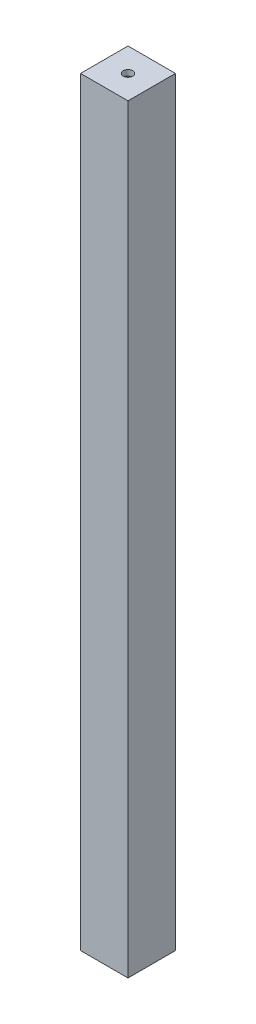
SolidWorks part; units mm, degrees
ref_plane "Front Plane" through (0, 0, 0) normal (0, 0, 1) x (1, 0, 0)
ref_plane "Top Plane" through (0, 0, 0) normal (0, 1, 0) x (1, 0, 0)
ref_plane "Right Plane" through (0, 0, 0) normal (1, 0, 0) x (0, 0, -1)
sketch "Sketch1" plane through (0, 0, 0) normal (0, 1, 0) x (1, 0, 0)
  line L1 (-12.5, 12.5) -> (12.5, 12.5)
  line L2 (-12.5, 12.5) -> (-12.5, -12.5)
  line L3 (-12.5, -12.5) -> (12.5, -12.5)
  line L4 (12.5, 12.5) -> (12.5, -12.5)
  line L5 (-12.5, 12.5) -> (12.5, -12.5) construction
  line L6 (-12.5, -12.5) -> (12.5, 12.5) construction
  point P0 (0, 0)
  dimension "D1" = 25
  dimension "D2" = 25
extrude "Boss-Extrude1" add sketch "Sketch1" along normal blind 400
shell "Shell1" thickness 3
sketch "Sketch2" plane through (0, 400, 0) normal (0, 1, 0) x (1, 0, 0)
  line L0 (-9.5, 9.5) -> (-9.5, -9.5) construction
  line L1 (-9.5, -9.5) -> (9.5, -9.5) construction
  line L2 (9.5, -9.5) -> (9.5, 9.5) construction
  line L3 (9.5, 9.5) -> (-9.5, 9.5) construction
  line L4 (-9.5, 9.5) -> (-9.5, -9.5)
  line L5 (-9.5, -9.5) -> (9.5, -9.5)
  line L6 (9.5, -9.5) -> (9.5, 9.5)
  line L7 (9.5, 9.5) -> (-9.5, 9.5)
  circle A0 centre (0, 0) radius 2.5
  dimension "D1" = 5
extrude "Boss-Extrude2" add sketch "Sketch2" against normal blind 3
